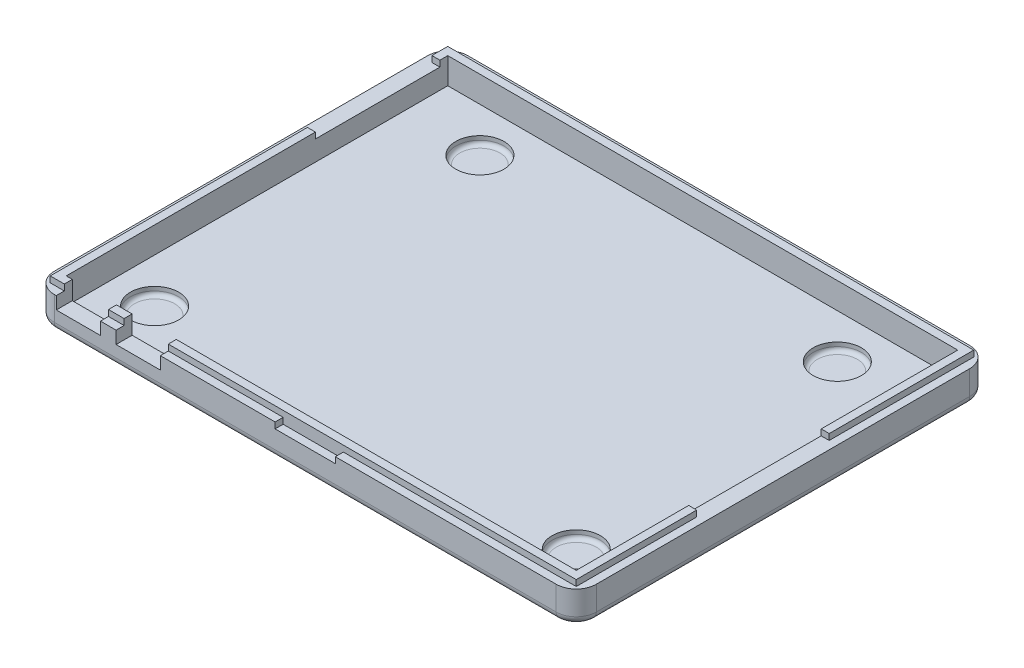
SolidWorks part; units mm, degrees
ref_plane "Front Plane" through (0, 0, 0) normal (0, 0, 1) x (1, 0, 0)
ref_plane "Top Plane" through (0, 0, 0) normal (0, 1, 0) x (1, 0, 0)
ref_plane "Right Plane" through (0, 0, 0) normal (1, 0, 0) x (0, 0, -1)
sketch "Sketch1" plane through (0, 0, 0) normal (0, 1, 0) x (1, 0, 0)
  line L1 (-67.5, 51.5) -> (67.5, 51.5)
  line L2 (-67.5, 51.5) -> (-67.5, -51.5)
  line L3 (-67.5, -51.5) -> (67.5, -51.5)
  line L4 (67.5, 51.5) -> (67.5, -51.5)
  line L5 (-67.5, 51.5) -> (67.5, -51.5) construction
  line L6 (-67.5, -51.5) -> (67.5, 51.5) construction
  point P0 (0, 0)
  dimension "D1" = 135
  dimension "D2" = 103
extrude "Boss-Extrude1" add sketch "Sketch1" along normal blind 13
sketch "Sketch2" plane through (0, 13, 0) normal (0, 1, 0) x (1, 0, 0)
  line L0 (67.5, -51.5) -> (67.5, 51.5) construction
  line L1 (-63.51, 47.51) -> (63.51, 47.51)
  line L2 (-63.51, 47.51) -> (-63.51, -47.51)
  line L3 (-63.51, -47.51) -> (63.51, -47.51)
  line L4 (63.51, 47.51) -> (63.51, -47.51)
  line L5 (-63.51, 47.51) -> (63.51, -47.51) construction
  line L6 (-63.51, -47.51) -> (63.51, 47.51) construction
  line L7 (-67.5, -51.5) -> (67.5, -51.5) construction
  point P0 (0, 0)
  dimension "D1" = 3.99
  dimension "D2" = 3.99
extrude "Cut-Extrude1" cut sketch "Sketch2" against normal blind 10
sketch "Sketch3" plane through (0, 3, 0) normal (0, 1, 0) x (1, 0, 0)
  line L0 (-63.51, 47.51) -> (-63.51, -47.51) construction
  line L1 (-63.51, -47.51) -> (63.51, -47.51) construction
  circle A0 centre (-52.51, -36.51) radius 6
  dimension "D3" = 12
  dimension "D1" = 11
  dimension "D2" = 11
extrude "Cut-Extrude2" cut sketch "Sketch3" against normal blind 2
fillet "Fillet1" radius 1 1 edges at (-52.51, 1, 42.51)
mirror "Mirror1" about plane through (0, 0, 0) normal (1, 0, 0) of "Fillet1", "Cut-Extrude2"
sketch "Sketch4" plane through (0, 3, 0) normal (0, 1, 0) x (1, 0, 0)
  line L2 (63.51, 47.51) -> (-63.51, 47.51) construction
  line L3 (-63.51, 47.51) -> (-63.51, -47.51) construction
  circle A0 centre (-44.51, 36.51) radius 6
  dimension "D3" = 12
  dimension "D1" = 11
  dimension "D2" = 19
extrude "Cut-Extrude3" cut sketch "Sketch4" against normal blind 2
fillet "Fillet2" radius 1 1 edges at (-44.51, 1, -30.51)
mirror "Mirror2" about plane through (0, 0, 0) normal (1, 0, 0) of "Fillet2", "Cut-Extrude3"
sketch "Sketch5" plane through (-67.5, 0, 0) normal (-1, 0, 0) x (0, 0, 1)
  line L0 (-51.5, 0) -> (51.5, 0) construction
  line L1 (-45.55, 10.5) -> (-14.55, 10.5)
  line L2 (-45.55, 10.5) -> (-45.55, 8)
  line L3 (-45.55, 8) -> (-14.55, 8)
  line L4 (-14.55, 10.5) -> (-14.55, 8)
  line L5 (-51.5, 13) -> (-51.5, 0) construction
  dimension "D1" = 8
  dimension "D2" = 5.95
  dimension "D3" = 31
  dimension "D4" = 2.5
extrude "Cut-Extrude4" cut sketch "Sketch5" against normal blind 5
sketch "Sketch6" plane through (0, 13, 0) normal (0, 1, 0) x (1, 0, 0)
  line L1 (-67.5, -51.5) -> (67.5, -51.5)
  line L2 (-67.5, -51.5) -> (-67.5, 51.5)
  line L3 (-67.5, 51.5) -> (67.5, 51.5)
  line L4 (67.5, -51.5) -> (67.5, 51.5)
extrude "Cut-Extrude5" cut sketch "Sketch6" against normal blind 3.5
sketch "Sketch7" plane through (67.5, 0, 0) normal (1, 0, 0) x (0, 0, -1)
  line L0 (-51.5, 9.5) -> (-51.5, 0) construction
  line L1 (-19.5, 20) -> (13.5, 20)
  line L2 (-19.5, 20) -> (-19.5, 8)
  line L3 (-19.5, 8) -> (13.5, 8)
  line L4 (13.5, 20) -> (13.5, 8)
  line L5 (-19.5, 20) -> (13.5, 8) construction
  line L6 (-19.5, 8) -> (13.5, 20) construction
  line L7 (-51.5, 0) -> (51.5, 0) construction
  point P0 (-3, 14)
  dimension "D1" = 32
  dimension "D2" = 33
  dimension "D3" = 8
  dimension "D4" = 12
extrude "Cut-Extrude6" cut sketch "Sketch7" against normal blind 5
sketch "Sketch8" plane through (0, 9.5, 0) normal (0, 1, 0) x (1, 0, 0)
  line L1 (-65.5, 49.5) -> (65.5, 49.5)
  line L2 (-65.5, 49.5) -> (-65.5, -49.5)
  line L3 (-65.5, -49.5) -> (65.5, -49.5)
  line L4 (65.5, 49.5) -> (65.5, -49.5)
  line L5 (-65.5, 49.5) -> (65.5, -49.5) construction
  line L6 (-65.5, -49.5) -> (65.5, 49.5) construction
  point P0 (0, 0)
  dimension "D1" = 131
  dimension "D2" = 99
extrude "Cut Around side for friction fitting cover" cut sketch "Sketch8" against normal blind 1.5 flip side to cut
sketch "Sketch9" plane through (0, 8, 0) normal (0, 1, 0) x (1, 0, 0)
  line L0 (-65.5, -49.5) -> (65.5, -49.5) construction
  line L1 (-7.5, -49.5) -> (7.5, -49.5)
  line L2 (-7.5, -49.5) -> (-7.5, -51.5)
  line L3 (-7.5, -51.5) -> (7.5, -51.5)
  line L4 (7.5, -49.5) -> (7.5, -51.5)
  line L5 (-67.5, -51.5) -> (67.5, -51.5) construction
  line L6 (-67.5, 51.5) -> (-67.5, -51.5) construction
  line L7 (67.5, -51.5) -> (67.5, 51.5) construction
  dimension "D1" = 60
  dimension "D2" = 60
extrude "Cut-Extrude8" cut sketch "Sketch9" against normal blind 1.5
ref_plane "Plane1" through (67.5, 8, -51.5) normal (0, 0, -1) x (-1, 0, 0)
sketch "Sketch10" plane through (67.5, 8, -51.5) normal (0, 0, -1) x (-1, 0, 0)
  line L0 (0, 0) -> (0, -8) construction
  line L1 (6, 1) -> (14, 1)
  line L2 (6, 1) -> (6, -3)
  line L3 (6, -3) -> (14, -3)
  line L4 (14, 1) -> (14, -3)
  line L5 (6, 1) -> (14, -3) construction
  line L6 (6, -3) -> (14, 1) construction
  line L7 (0, -8) -> (135, -8) construction
  point P0 (10, -1)
  dimension "D1" = 6
  dimension "D2" = 5
  dimension "D3" = 4
  dimension "D4" = 8
extrude "Cut-Extrude10" [suppressed] cut sketch "Sketch10" against normal blind 5
sketch "Sketch11" [suppressed] plane through (0, 0, -51.5) normal (0, 0, -1) x (-1, 0, 0)
  line L0 (-67.5, 5) -> (67.5, 5) construction
  line L1 (-45.5, 9) -> (-37.5, 9)
  line L2 (-45.5, 9) -> (-45.5, 5)
  line L3 (-45.5, 5) -> (-37.5, 5)
  line L4 (-37.5, 9) -> (-37.5, 5)
  line L5 (-45.5, 9) -> (-37.5, 5) construction
  line L6 (-45.5, 5) -> (-37.5, 9) construction
  line L7 (-53.5, 5) -> (-53.5, 6.5) construction
  point P0 (-41.5, 7)
  dimension "D1" = 8
  dimension "D2" = 8
  dimension "D3" = 4
extrude "Cut-Extrude11" [suppressed] cut sketch "Sketch11" against normal blind 5
fillet "Fillet3" radius 5 4 edges at (67.5, 4, 51.5) (67.5, 4, -51.5) (-67.5, 4, -51.5) (-67.5, 4, 51.5)
fillet "Fillet4" radius 2 8 edges at (-66.0355, 0, -50.0355) (0, 0, -51.5) (66.0355, 0, -50.0355) (67.5, 0, 0) (66.0355, 0, 50.0355) (0, 0, 51.5) (-66.0355, 0, 50.0355) (-67.5, 0, 0)
sketch "Sketch14" plane through (0, 0, 49.5) normal (0, 0, 1) x (1, 0, 0)
  line L0 (-65.5, 9.5) -> (65.5, 9.5) construction
  line L1 (-60.6, 9.5) -> (-52.4, 9.5)
  line L2 (-60.6, 9.5) -> (-60.6, 8)
  line L3 (-60.6, 8) -> (-52.4, 8)
  line L4 (-52.4, 9.5) -> (-52.4, 8)
  line L5 (-65.5, 8) -> (-7.5, 8) construction
  line L6 (-65.5, 8) -> (-65.5, 9.5) construction
  dimension "D1" = 4.9
  dimension "D2" = 8.2
extrude "Cut-Extrude13" cut sketch "Sketch14" against normal blind 4
sketch "Sketch16" plane through (0, 0, 49.5) normal (0, 0, 1) x (1, 0, 0)
  line L0 (-52.4, 9.5) -> (65.5, 9.5) construction
  line L1 (-45.6, 9.5) -> (-37.4, 9.5)
  line L2 (-45.6, 9.5) -> (-45.6, 8)
  line L3 (-45.6, 8) -> (-37.4, 8)
  line L4 (-37.4, 9.5) -> (-37.4, 8)
  line L6 (-62.5, 8) -> (-7.5, 8) construction
  line L7 (-67.5, 2) -> (-67.5, 8) construction
  point P6 (-37.4, 8)
  point P10 (0, 0)
  dimension "D1" = 21.9
  dimension "D2" = 8.2
extrude "Cut-Extrude14" cut sketch "Sketch16" against normal blind 4
sketch "Sketch17" plane through (-60.6, 0, 0) normal (1, 0, 0) x (0, 0, -1)
  line L1 (-49.5, 9.5) -> (-47.51, 9.5)
  line L2 (-49.5, 9.5) -> (-49.5, 8)
  line L3 (-49.5, 8) -> (-47.51, 8)
  line L4 (-47.51, 9.5) -> (-47.51, 8)
extrude "Cut-Extrude15" cut sketch "Sketch17" against normal blind 1.1 and the other way blind 9.3
sketch "Sketch18" plane through (-45.6, 0, 0) normal (1, 0, 0) x (0, 0, -1)
  line L1 (-49.5, 9.5) -> (-47.51, 9.5)
  line L2 (-49.5, 9.5) -> (-49.5, 8)
  line L3 (-49.5, 8) -> (-47.51, 8)
  line L4 (-47.51, 9.5) -> (-47.51, 8)
extrude "Cut-Extrude16" cut sketch "Sketch18" against normal blind 1.1 and the other way blind 9.3
sketch "Sketch19" plane through (0, 8, 0) normal (0, 1, 0) x (1, 0, 0)
  line L1 (-61.7, -47.51) -> (-51.3, -47.51)
  line L2 (-61.7, -47.51) -> (-61.7, -52.2025)
  line L3 (-61.7, -52.2025) -> (-51.3, -52.2025)
  line L4 (-51.3, -47.51) -> (-51.3, -52.2025)
  line L5 (-46.7, -47.51) -> (-36.2307, -47.51)
  line L6 (-46.7, -47.51) -> (-46.7, -52.7558)
  line L7 (-46.7, -52.7558) -> (-36.2307, -52.7558)
  line L8 (-36.2307, -47.51) -> (-36.2307, -52.7558)
extrude "Cut-Extrude17" cut sketch "Sketch19" against normal blind 3.1
sketch "Sketch20" plane through (0, 9.5, 0) normal (0, 1, 0) x (1, 0, 0)
  line L1 (-51.3, -47.51) -> (-46.7, -47.51)
  line L2 (-51.3, -47.51) -> (-51.3, -51.5)
  line L3 (-51.3, -51.5) -> (-46.7, -51.5)
  line L4 (-46.7, -47.51) -> (-46.7, -51.5)
extrude "Cut-Extrude18" [suppressed] cut sketch "Sketch20" against normal blind 4.6
sketch "Sketch23" plane through (-36.2307, 0, 0) normal (-1, 0, 0) x (0, 0, 1)
  line L0 (47.51, 4.9) -> (47.51, 8)
  line L1 (47.51, 4.9) -> (47.51, 8) construction
  line L2 (49.5, 8) -> (47.51, 8) construction
  line L3 (47.51, 8) -> (51.5, 8)
  line L4 (51.5, 8) -> (51.5, 4.9)
  line L5 (51.5, 4.9) -> (47.51, 4.9)
extrude "Boss-Extrude2" add sketch "Sketch23" along normal blind 0.0693
sketch "Sketch24" plane through (-36.3, 0, 0) normal (-1, 0, 0) x (0, 0, 1)
  line L0 (47.51, 4.9) -> (47.51, 9.5)
  line L1 (47.51, 9.5) -> (49.5, 9.5)
  line L2 (49.5, 9.5) -> (49.5, 8)
  line L3 (49.5, 8) -> (51.5, 8)
  line L4 (51.5, 8) -> (51.5, 4.9)
  line L5 (51.5, 4.9) -> (47.51, 4.9)
extrude "Cut-Extrude20" cut sketch "Sketch24" against normal blind 0.2
sketch "Sketch25" plane through (-46.7, 0, 0) normal (1, 0, 0) x (0, 0, -1)
  line L0 (-51.5, 4.9) -> (-47.51, 4.9)
  line L1 (-47.51, 4.9) -> (-47.51, 9.5)
  line L2 (-47.51, 9.5) -> (-49.5, 9.5)
  line L3 (-49.5, 9.5) -> (-49.5, 8)
  line L4 (-49.5, 8) -> (-51.5, 8)
  line L5 (-51.5, 8) -> (-51.5, 4.9)
extrude "Cut-Extrude21" cut sketch "Sketch25" against normal blind 0.4
sketch "Sketch26" plane through (-51.3, 0, 0) normal (-1, 0, 0) x (0, 0, 1)
  line L0 (47.51, 9.5) -> (47.51, 4.9)
  line L1 (47.51, 4.9) -> (51.5, 4.9)
  line L2 (51.5, 4.9) -> (51.5, 8)
  line L3 (51.5, 8) -> (49.5, 8)
  line L4 (49.5, 8) -> (49.5, 9.5)
  line L5 (49.5, 9.5) -> (47.51, 9.5)
extrude "Cut-Extrude22" cut sketch "Sketch26" against normal blind 0.3
sketch "Sketch27" plane through (-61.7, 0, 0) normal (1, 0, 0) x (0, 0, -1)
  line L0 (-51.5, 4.9) -> (-47.51, 4.9)
  line L1 (-47.51, 4.9) -> (-47.51, 9.5)
  line L2 (-47.51, 9.5) -> (-49.5, 9.5)
  line L3 (-49.5, 9.5) -> (-49.5, 8)
  line L4 (-49.5, 8) -> (-51.5, 8)
  line L5 (-51.5, 8) -> (-51.5, 4.9)
extrude "Cut-Extrude23" cut sketch "Sketch27" against normal blind 0.3
scale "Scale1" scale about origin uniform scaling yes scale factor 1.015
